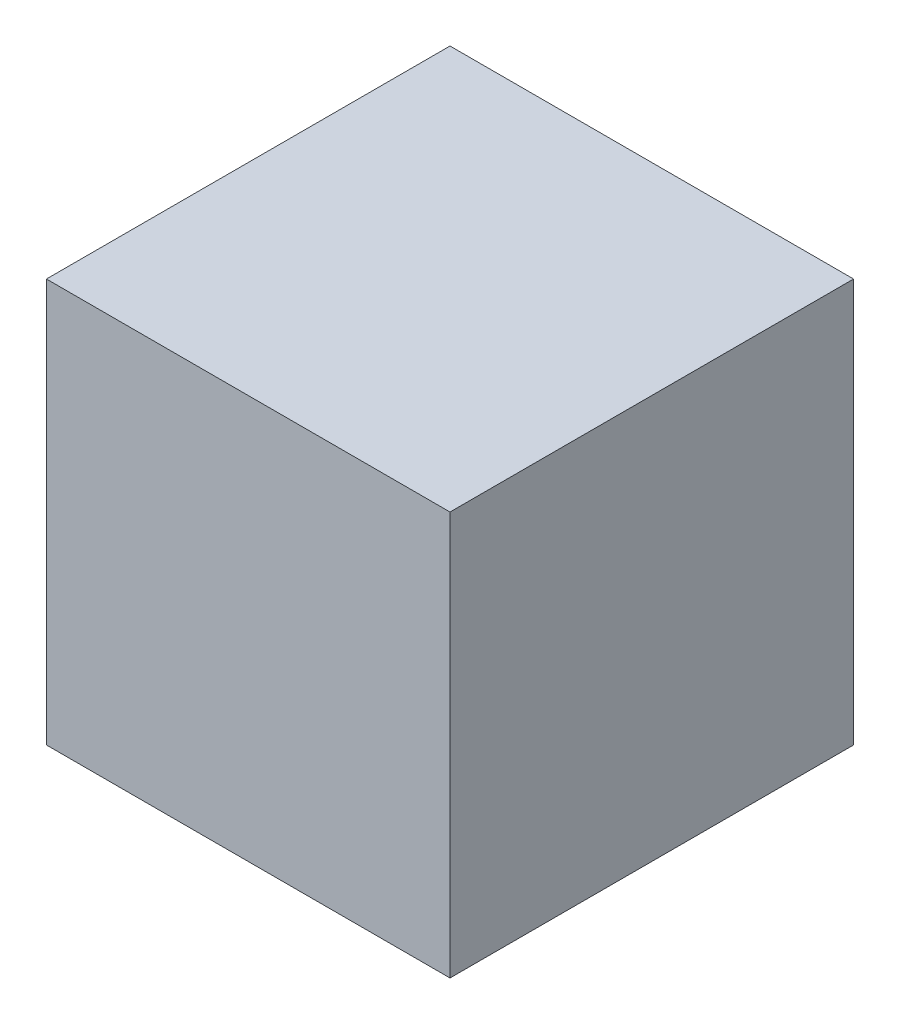
SolidWorks part; units mm, degrees
material "普通碳钢"
ref_plane "前视基准面" through (0, 0, 0) normal (0, 0, 1) x (1, 0, 0)
ref_plane "上视基准面" through (0, 0, 0) normal (0, 1, 0) x (1, 0, 0)
ref_plane "右视基准面" through (0, 0, 0) normal (1, 0, 0) x (0, 0, -1)
sketch "草图1" plane through (0, 0, 0) normal (0, 0, 1) x (1, 0, 0)
  line L0 (0, 0) -> (-78.598, 0) construction
  line L1 (0, 0) -> (0, 95.883) construction
  line L2 (0, -55) -> (0, 55) construction
  point P0 (0, 0)
sketch "草图2" plane through (0, 0, 0) normal (0, 0, 1) x (1, 0, 0)
  line L1 (-0.05, 0.05) -> (0.05, 0.05)
  line L2 (-0.05, 0.05) -> (-0.05, -0.05)
  line L3 (-0.05, -0.05) -> (0.05, -0.05)
  line L4 (0.05, 0.05) -> (0.05, -0.05)
  line L5 (-0.05, 0.05) -> (0.05, -0.05) construction
  line L6 (-0.05, -0.05) -> (0.05, 0.05) construction
  point P0 (0, 0)
  dimension "D1" = 0.1
  dimension "D2" = 0.1
extrude "凸台-拉伸1" add sketch "草图2" along normal mid plane 0.1
